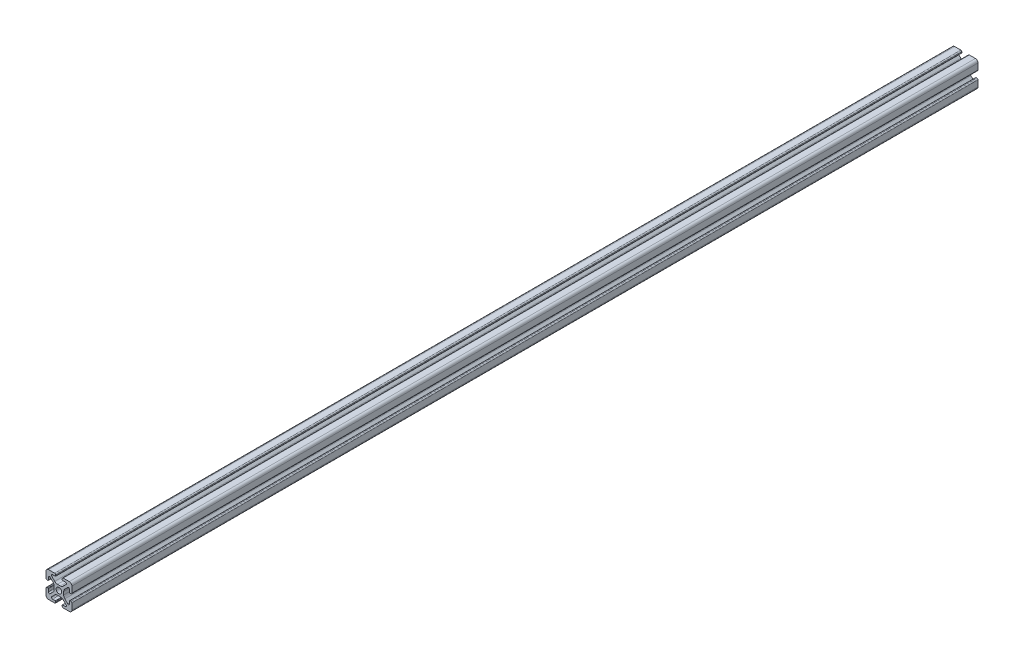
SolidWorks part; units mm, degrees
ref_plane "Front" through (0, 0, 0) normal (0, 0, 1) x (1, 0, 0)
ref_plane "Top" through (0, 0, 0) normal (0, 1, 0) x (1, 0, 0)
ref_plane "Right" through (0, 0, 0) normal (1, 0, 0) x (0, 0, -1)
sketch "Support-Front" plane through (0, 0, 0) normal (0, 0, 1) x (1, 0, 0)
  line L0 (10, 0) -> (-10, 0) construction
  line L1 (-10, -10) -> (10, -10)
  line L2 (-10, -10) -> (-10, 10)
  line L3 (-10, 10) -> (10, 10)
  line L4 (10, -10) -> (10, 10)
  line L5 (0, 10) -> (0, -10) construction
  dimension "Height-Profile" = 20
  dimension "Width-Profile" = 20
sketch "Support-Right-Length" plane through (0, 0, 0) normal (1, 0, 0) x (0, 0, -1)
  line L0 (0, -10) -> (0, 10) construction
  line L1 (-25, 10) -> (25, 10)
  line L2 (-25, 10) -> (-25, -10)
  line L3 (-25, -10) -> (25, -10)
  line L4 (25, 10) -> (25, -10)
  dimension "Length-Profile" = 50
sketch "Support-Profile" plane through (0, 0, 0) normal (0, 0, 1) x (1, 0, 0)
  line L8 (4.9176, -8.2) -> (2.8, -8.2)
  line L9 (2.5, -8.5) -> (2.5, -9.2)
  line L10 (3.3, -10) -> (8, -10)
  line L11 (10, -8) -> (10, -3.3)
  line L24 (9.2, -2.5) -> (8.5, -2.5)
  line L25 (8.2, -2.8) -> (8.2, -4.9176)
  line L26 (6.779, -5.5062) -> (4.5287, -3.2559)
  line L27 (3.65, -1.1346) -> (3.65, 1.1346)
  line L28 (4.5287, 3.2559) -> (6.779, 5.5062)
  line L29 (8.2, 4.9176) -> (8.2, 2.8)
  line L30 (8.5, 2.5) -> (9.2, 2.5)
  line L31 (10, 3.3) -> (10, 8)
  line L32 (8, 10) -> (3.3, 10)
  line L33 (2.5, 9.2) -> (2.5, 8.5)
  line L34 (2.8, 8.2) -> (4.9176, 8.2)
  line L35 (5.5062, 6.779) -> (3.2559, 4.5287)
  line L40 (1.1346, 3.65) -> (-1.1346, 3.65)
  line L41 (-3.2559, 4.5287) -> (-5.5062, 6.779)
  line L42 (-4.9176, 8.2) -> (-2.8, 8.2)
  line L43 (-2.5, 8.5) -> (-2.5, 9.2)
  line L44 (-3.3, 10) -> (-8, 10)
  line L45 (-10, 8) -> (-10, 3.3)
  line L46 (-9.2, 2.5) -> (-8.5, 2.5)
  line L47 (-8.2, 2.8) -> (-8.2, 4.9176)
  line L48 (-6.779, 5.5062) -> (-4.5287, 3.2559)
  line L49 (-3.65, 1.1346) -> (-3.65, -1.1346)
  line L50 (-4.5287, -3.2559) -> (-6.779, -5.5062)
  line L51 (-8.2, -4.9176) -> (-8.2, -2.8)
  line L52 (-8.5, -2.5) -> (-9.2, -2.5)
  line L53 (-10, -3.3) -> (-10, -8)
  line L54 (-8, -10) -> (-3.3, -10)
  line L55 (-2.5, -9.2) -> (-2.5, -8.5)
  line L56 (-2.8, -8.2) -> (-4.9176, -8.2)
  line L57 (-5.5062, -6.779) -> (-3.2559, -4.5287)
  line L58 (-1.1346, -3.65) -> (1.1346, -3.65)
  line L59 (3.2559, -4.5287) -> (5.5062, -6.779)
  circle A2 centre (0, 0) radius 2.15
  arc A3 (2.8, -8.2) -> (2.5, -8.5) centre (2.8, -8.5) ccw
  arc A5 (2.5, -9.2) -> (3.3, -10) centre (3.3, -9.2) ccw
  arc A24 (8, -10) -> (10, -8) centre (8, -8) ccw
  arc A25 (10, -3.3) -> (9.2, -2.5) centre (9.2, -3.3) ccw
  arc A26 (8.5, -2.5) -> (8.2, -2.8) centre (8.5, -2.8) ccw
  arc A27 (6.779, -5.5062) -> (8.2, -4.9176) centre (7.3676, -4.9176) ccw
  arc A28 (3.65, -1.1346) -> (4.5287, -3.2559) centre (6.65, -1.1346) ccw
  arc A29 (4.5287, 3.2559) -> (3.65, 1.1346) centre (6.65, 1.1346) ccw
  arc A30 (8.2, 4.9176) -> (6.779, 5.5062) centre (7.3676, 4.9176) ccw
  arc A31 (8.2, 2.8) -> (8.5, 2.5) centre (8.5, 2.8) ccw
  arc A32 (9.2, 2.5) -> (10, 3.3) centre (9.2, 3.3) ccw
  arc A33 (10, 8) -> (8, 10) centre (8, 8) ccw
  arc A34 (3.3, 10) -> (2.5, 9.2) centre (3.3, 9.2) ccw
  arc A35 (2.5, 8.5) -> (2.8, 8.2) centre (2.8, 8.5) ccw
  arc A38 (5.5062, 6.779) -> (4.9176, 8.2) centre (4.9176, 7.3676) ccw
  arc A39 (1.1346, 3.65) -> (3.2559, 4.5287) centre (1.1346, 6.65) ccw
  arc A44 (-3.2559, 4.5287) -> (-1.1346, 3.65) centre (-1.1346, 6.65) ccw
  arc A45 (-4.9176, 8.2) -> (-5.5062, 6.779) centre (-4.9176, 7.3676) ccw
  arc A46 (-2.8, 8.2) -> (-2.5, 8.5) centre (-2.8, 8.5) ccw
  arc A47 (-2.5, 9.2) -> (-3.3, 10) centre (-3.3, 9.2) ccw
  arc A48 (-8, 10) -> (-10, 8) centre (-8, 8) ccw
  arc A49 (-10, 3.3) -> (-9.2, 2.5) centre (-9.2, 3.3) ccw
  arc A50 (-8.5, 2.5) -> (-8.2, 2.8) centre (-8.5, 2.8) ccw
  arc A51 (-6.779, 5.5062) -> (-8.2, 4.9176) centre (-7.3676, 4.9176) ccw
  arc A52 (-3.65, 1.1346) -> (-4.5287, 3.2559) centre (-6.65, 1.1346) ccw
  arc A53 (-4.5287, -3.2559) -> (-3.65, -1.1346) centre (-6.65, -1.1346) ccw
  arc A54 (-8.2, -4.9176) -> (-6.779, -5.5062) centre (-7.3676, -4.9176) ccw
  arc A55 (-8.2, -2.8) -> (-8.5, -2.5) centre (-8.5, -2.8) ccw
  arc A56 (-9.2, -2.5) -> (-10, -3.3) centre (-9.2, -3.3) ccw
  arc A57 (-10, -8) -> (-8, -10) centre (-8, -8) ccw
  arc A58 (-3.3, -10) -> (-2.5, -9.2) centre (-3.3, -9.2) ccw
  arc A59 (-2.5, -8.5) -> (-2.8, -8.2) centre (-2.8, -8.5) ccw
  arc A60 (-5.5062, -6.779) -> (-4.9176, -8.2) centre (-4.9176, -7.3676) ccw
  arc A61 (-1.1346, -3.65) -> (-3.2559, -4.5287) centre (-1.1346, -6.65) ccw
  arc A62 (3.2559, -4.5287) -> (1.1346, -3.65) centre (1.1346, -6.65) ccw
  arc A63 (4.9176, -8.2) -> (5.5062, -6.779) centre (4.9176, -7.3676) ccw
ref_plane "Ref-Plane-1" through (0, 0, 25) normal (0, 0, 1) x (1, 0, 0)
ref_plane "Ref-Plane-2" through (0, 0, -25) normal (0, 0, 1) x (1, 0, 0)
sketch "Sketch4" plane through (0, 0, 25) normal (0, 0, 1) x (1, 0, 0)
  line L0 (-10, -10) -> (-10, 10) construction
  line L1 (-10, -10) -> (10, -10) construction
  line L2 (10, -10) -> (10, 10) construction
  line L3 (-10, 10) -> (10, 10) construction
  line L4 (-10, -10) -> (-10, 10)
  line L5 (-10, -10) -> (10, -10)
  line L6 (10, -10) -> (10, 10)
  line L7 (-10, 10) -> (10, 10)
extrude "Body" add sketch "Sketch4" against normal blind 700
sketch "Sketch16" plane through (0, 0, 0) normal (0, 0, 1) x (1, 0, 0)
  line L40 (4.9176, -8.2) -> (2.8, -8.2)
  line L41 (2.5, -8.5) -> (2.5, -9.2)
  line L42 (3.3, -10) -> (8, -10)
  line L43 (10, -8) -> (10, -3.3)
  line L44 (9.2, -2.5) -> (8.5, -2.5)
  line L45 (8.2, -2.8) -> (8.2, -4.9176)
  line L46 (6.779, -5.5062) -> (4.5287, -3.2559)
  line L47 (3.65, -1.1346) -> (3.65, 1.1346)
  line L48 (4.5287, 3.2559) -> (6.779, 5.5062)
  line L49 (8.2, 4.9176) -> (8.2, 2.8)
  line L50 (8.5, 2.5) -> (9.2, 2.5)
  line L51 (10, 3.3) -> (10, 8)
  line L52 (8, 10) -> (3.3, 10)
  line L53 (2.5, 9.2) -> (2.5, 8.5)
  line L54 (2.8, 8.2) -> (4.9176, 8.2)
  line L55 (5.5062, 6.779) -> (3.2559, 4.5287)
  line L56 (1.1346, 3.65) -> (-1.1346, 3.65)
  line L57 (-3.2559, 4.5287) -> (-5.5062, 6.779)
  line L58 (-4.9176, 8.2) -> (-2.8, 8.2)
  line L59 (-2.5, 8.5) -> (-2.5, 9.2)
  line L60 (-3.3, 10) -> (-8, 10)
  line L61 (-10, 8) -> (-10, 3.3)
  line L62 (-9.2, 2.5) -> (-8.5, 2.5)
  line L63 (-8.2, 2.8) -> (-8.2, 4.9176)
  line L64 (-6.779, 5.5062) -> (-4.5287, 3.2559)
  line L65 (-3.65, 1.1346) -> (-3.65, -1.1346)
  line L66 (-4.5287, -3.2559) -> (-6.779, -5.5062)
  line L67 (-8.2, -4.9176) -> (-8.2, -2.8)
  line L68 (-8.5, -2.5) -> (-9.2, -2.5)
  line L69 (-10, -3.3) -> (-10, -8)
  line L70 (-8, -10) -> (-3.3, -10)
  line L71 (-2.5, -9.2) -> (-2.5, -8.5)
  line L72 (-2.8, -8.2) -> (-4.9176, -8.2)
  line L73 (-5.5062, -6.779) -> (-3.2559, -4.5287)
  line L74 (-1.1346, -3.65) -> (1.1346, -3.65)
  line L75 (3.2559, -4.5287) -> (5.5062, -6.779)
  line L76 (4.9176, -8.2) -> (2.8, -8.2)
  line L77 (2.5, -8.5) -> (2.5, -9.2)
  line L78 (3.3, -10) -> (8, -10)
  line L79 (10, -8) -> (10, -3.3)
  line L80 (9.2, -2.5) -> (8.5, -2.5)
  line L81 (8.2, -2.8) -> (8.2, -4.9176)
  line L82 (6.779, -5.5062) -> (4.5287, -3.2559)
  line L83 (3.65, -1.1346) -> (3.65, 1.1346)
  line L84 (4.5287, 3.2559) -> (6.779, 5.5062)
  line L85 (8.2, 4.9176) -> (8.2, 2.8)
  line L86 (8.5, 2.5) -> (9.2, 2.5)
  line L87 (10, 3.3) -> (10, 8)
  line L88 (8, 10) -> (3.3, 10)
  line L89 (2.5, 9.2) -> (2.5, 8.5)
  line L90 (2.8, 8.2) -> (4.9176, 8.2)
  line L91 (5.5062, 6.779) -> (3.2559, 4.5287)
  line L92 (1.1346, 3.65) -> (-1.1346, 3.65)
  line L93 (-3.2559, 4.5287) -> (-5.5062, 6.779)
  line L94 (-4.9176, 8.2) -> (-2.8, 8.2)
  line L95 (-2.5, 8.5) -> (-2.5, 9.2)
  line L96 (-3.3, 10) -> (-8, 10)
  line L97 (-10, 8) -> (-10, 3.3)
  line L98 (-9.2, 2.5) -> (-8.5, 2.5)
  line L99 (-8.2, 2.8) -> (-8.2, 4.9176)
  line L100 (-6.779, 5.5062) -> (-4.5287, 3.2559)
  line L101 (-3.65, 1.1346) -> (-3.65, -1.1346)
  line L102 (-4.5287, -3.2559) -> (-6.779, -5.5062)
  line L103 (-8.2, -4.9176) -> (-8.2, -2.8)
  line L104 (-8.5, -2.5) -> (-9.2, -2.5)
  line L105 (-10, -3.3) -> (-10, -8)
  line L106 (-8, -10) -> (-3.3, -10)
  line L107 (-2.5, -9.2) -> (-2.5, -8.5)
  line L108 (-2.8, -8.2) -> (-4.9176, -8.2)
  line L109 (-5.5062, -6.779) -> (-3.2559, -4.5287)
  line L110 (-1.1346, -3.65) -> (1.1346, -3.65)
  line L111 (3.2559, -4.5287) -> (5.5062, -6.779)
  circle A7 centre (0, 0) radius 2.15 construction
  circle A8 centre (0, 0) radius 2.15
  arc A43 (2.8, -8.2) -> (2.5, -8.5) centre (2.8, -8.5) ccw
  arc A44 (2.5, -9.2) -> (3.3, -10) centre (3.3, -9.2) ccw
  arc A45 (8, -10) -> (10, -8) centre (8, -8) ccw
  arc A46 (10, -3.3) -> (9.2, -2.5) centre (9.2, -3.3) ccw
  arc A47 (8.5, -2.5) -> (8.2, -2.8) centre (8.5, -2.8) ccw
  arc A48 (6.779, -5.5062) -> (8.2, -4.9176) centre (7.3676, -4.9176) ccw
  arc A49 (3.65, -1.1346) -> (4.5287, -3.2559) centre (6.65, -1.1346) ccw
  arc A50 (4.5287, 3.2559) -> (3.65, 1.1346) centre (6.65, 1.1346) ccw
  arc A51 (8.2, 4.9176) -> (6.779, 5.5062) centre (7.3676, 4.9176) ccw
  arc A52 (8.2, 2.8) -> (8.5, 2.5) centre (8.5, 2.8) ccw
  arc A53 (9.2, 2.5) -> (10, 3.3) centre (9.2, 3.3) ccw
  arc A54 (10, 8) -> (8, 10) centre (8, 8) ccw
  arc A55 (3.3, 10) -> (2.5, 9.2) centre (3.3, 9.2) ccw
  arc A56 (2.5, 8.5) -> (2.8, 8.2) centre (2.8, 8.5) ccw
  arc A57 (5.5062, 6.779) -> (4.9176, 8.2) centre (4.9176, 7.3676) ccw
  arc A58 (1.1346, 3.65) -> (3.2559, 4.5287) centre (1.1346, 6.65) ccw
  arc A59 (-3.2559, 4.5287) -> (-1.1346, 3.65) centre (-1.1346, 6.65) ccw
  arc A60 (-4.9176, 8.2) -> (-5.5062, 6.779) centre (-4.9176, 7.3676) ccw
  arc A61 (-2.8, 8.2) -> (-2.5, 8.5) centre (-2.8, 8.5) ccw
  arc A62 (-2.5, 9.2) -> (-3.3, 10) centre (-3.3, 9.2) ccw
  arc A63 (-8, 10) -> (-10, 8) centre (-8, 8) ccw
  arc A64 (-10, 3.3) -> (-9.2, 2.5) centre (-9.2, 3.3) ccw
  arc A65 (-8.5, 2.5) -> (-8.2, 2.8) centre (-8.5, 2.8) ccw
  arc A66 (-6.779, 5.5062) -> (-8.2, 4.9176) centre (-7.3676, 4.9176) ccw
  arc A67 (-3.65, 1.1346) -> (-4.5287, 3.2559) centre (-6.65, 1.1346) ccw
  arc A68 (-4.5287, -3.2559) -> (-3.65, -1.1346) centre (-6.65, -1.1346) ccw
  arc A69 (-8.2, -4.9176) -> (-6.779, -5.5062) centre (-7.3676, -4.9176) ccw
  arc A70 (-8.2, -2.8) -> (-8.5, -2.5) centre (-8.5, -2.8) ccw
  arc A71 (-9.2, -2.5) -> (-10, -3.3) centre (-9.2, -3.3) ccw
  arc A72 (-10, -8) -> (-8, -10) centre (-8, -8) ccw
  arc A73 (-3.3, -10) -> (-2.5, -9.2) centre (-3.3, -9.2) ccw
  arc A74 (-2.5, -8.5) -> (-2.8, -8.2) centre (-2.8, -8.5) ccw
  arc A75 (-5.5062, -6.779) -> (-4.9176, -8.2) centre (-4.9176, -7.3676) ccw
  arc A76 (-1.1346, -3.65) -> (-3.2559, -4.5287) centre (-1.1346, -6.65) ccw
  arc A77 (3.2559, -4.5287) -> (1.1346, -3.65) centre (1.1346, -6.65) ccw
  arc A78 (4.9176, -8.2) -> (5.5062, -6.779) centre (4.9176, -7.3676) ccw
  arc A79 (2.8, -8.2) -> (2.5, -8.5) centre (2.8, -8.5) ccw
  arc A80 (2.5, -9.2) -> (3.3, -10) centre (3.3, -9.2) ccw
  arc A81 (8, -10) -> (10, -8) centre (8, -8) ccw
  arc A82 (10, -3.3) -> (9.2, -2.5) centre (9.2, -3.3) ccw
  arc A83 (8.5, -2.5) -> (8.2, -2.8) centre (8.5, -2.8) ccw
  arc A84 (6.779, -5.5062) -> (8.2, -4.9176) centre (7.3676, -4.9176) ccw
  arc A85 (3.65, -1.1346) -> (4.5287, -3.2559) centre (6.65, -1.1346) ccw
  arc A86 (4.5287, 3.2559) -> (3.65, 1.1346) centre (6.65, 1.1346) ccw
  arc A87 (8.2, 4.9176) -> (6.779, 5.5062) centre (7.3676, 4.9176) ccw
  arc A88 (8.2, 2.8) -> (8.5, 2.5) centre (8.5, 2.8) ccw
  arc A89 (9.2, 2.5) -> (10, 3.3) centre (9.2, 3.3) ccw
  arc A90 (10, 8) -> (8, 10) centre (8, 8) ccw
  arc A91 (3.3, 10) -> (2.5, 9.2) centre (3.3, 9.2) ccw
  arc A92 (2.5, 8.5) -> (2.8, 8.2) centre (2.8, 8.5) ccw
  arc A93 (5.5062, 6.779) -> (4.9176, 8.2) centre (4.9176, 7.3676) ccw
  arc A94 (1.1346, 3.65) -> (3.2559, 4.5287) centre (1.1346, 6.65) ccw
  arc A95 (-3.2559, 4.5287) -> (-1.1346, 3.65) centre (-1.1346, 6.65) ccw
  arc A96 (-4.9176, 8.2) -> (-5.5062, 6.779) centre (-4.9176, 7.3676) ccw
  arc A97 (-2.8, 8.2) -> (-2.5, 8.5) centre (-2.8, 8.5) ccw
  arc A98 (-2.5, 9.2) -> (-3.3, 10) centre (-3.3, 9.2) ccw
  arc A99 (-8, 10) -> (-10, 8) centre (-8, 8) ccw
  arc A100 (-10, 3.3) -> (-9.2, 2.5) centre (-9.2, 3.3) ccw
  arc A101 (-8.5, 2.5) -> (-8.2, 2.8) centre (-8.5, 2.8) ccw
  arc A102 (-6.779, 5.5062) -> (-8.2, 4.9176) centre (-7.3676, 4.9176) ccw
  arc A103 (-3.65, 1.1346) -> (-4.5287, 3.2559) centre (-6.65, 1.1346) ccw
  arc A104 (-4.5287, -3.2559) -> (-3.65, -1.1346) centre (-6.65, -1.1346) ccw
  arc A105 (-8.2, -4.9176) -> (-6.779, -5.5062) centre (-7.3676, -4.9176) ccw
  arc A106 (-8.2, -2.8) -> (-8.5, -2.5) centre (-8.5, -2.8) ccw
  arc A107 (-9.2, -2.5) -> (-10, -3.3) centre (-9.2, -3.3) ccw
  arc A108 (-10, -8) -> (-8, -10) centre (-8, -8) ccw
  arc A109 (-3.3, -10) -> (-2.5, -9.2) centre (-3.3, -9.2) ccw
  arc A110 (-2.5, -8.5) -> (-2.8, -8.2) centre (-2.8, -8.5) ccw
  arc A111 (-5.5062, -6.779) -> (-4.9176, -8.2) centre (-4.9176, -7.3676) ccw
  arc A112 (-1.1346, -3.65) -> (-3.2559, -4.5287) centre (-1.1346, -6.65) ccw
  arc A113 (3.2559, -4.5287) -> (1.1346, -3.65) centre (1.1346, -6.65) ccw
  arc A114 (4.9176, -8.2) -> (5.5062, -6.779) centre (4.9176, -7.3676) ccw
  dimension "D1" = 0
extrude "Cut-Profile" cut sketch "Sketch16" against normal through all and the other way through all flip side to cut
